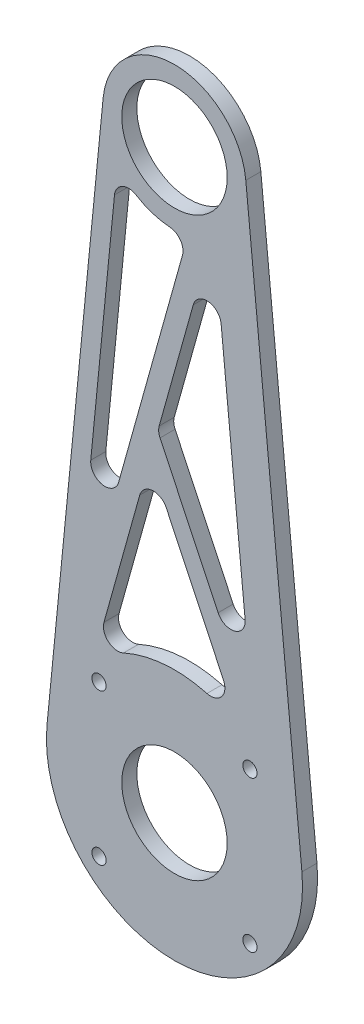
SolidWorks part; units mm, degrees
ref_plane "Front Plane" through (0, 0, 0) normal (0, 0, 1) x (1, 0, 0)
ref_plane "Top Plane" through (0, 0, 0) normal (0, 1, 0) x (1, 0, 0)
ref_plane "Right Plane" through (0, 0, 0) normal (1, 0, 0) x (0, 0, -1)
sketch "Sketch1" plane through (0, 0, 0) normal (0, 0, 1) x (1, 0, 0)
  line L0 (-15.04, 122.9996) -> (-26.8705, 2.6412)
  line L1 (15.04, 122.9996) -> (26.8705, 2.6412)
  circle A1 centre (15.9099, 15.9099) radius 1.5
  circle A2 centre (15.9099, -15.9099) radius 1.5
  circle A3 centre (-15.9099, -15.9099) radius 1.5
  circle A4 centre (-15.9099, 15.9099) radius 1.5
  circle A5 centre (0, 0) radius 27
  circle A6 centre (0, 121.5212) radius 11.1125
  circle A7 centre (0, 121.5212) radius 15.1125
  circle A8 centre (0, 0) radius 11.1125
  point P14 (0, 0)
  dimension "D2" = 3
  dimension "D4" = 54
  dimension "D5" = 22.225
  dimension "D8" = 22.225
  dimension "D7" = 121.5212
  dimension "D6" = 4
  dimension "D3" = 4
extrude "Boss-Extrude1" add sketch "Sketch1" along normal blind 3.175 contours A5 A8 A1 A2 A3 A4 | A7 L0 A5 L1 | A7 A6
sketch "Sketch2" plane through (0, 0, 0) normal (0, 0, -1) x (-1, 0, 0)
  line L5 (21.0059, 21.4147) -> (-2.8164, 106.6735)
  line L6 (22.8897, 2.2499) -> (11.0592, 122.6083)
  line L7 (-11.0592, 122.6083) -> (-22.8897, 2.2499)
  line L8 (21.0059, 21.4147) -> (12.0611, 112.4153)
  line L11 (2.5385, 65.8517) -> (3.525, 67.9304)
  line L12 (-8.2664, 110.131) -> (-16.5783, 25.5689)
  line L13 (3.525, 67.9304) -> (-8.2664, 110.131)
  line L14 (2.5385, 65.8517) -> (-16.5783, 25.5689)
  line L15 (16.9571, 19.8575) -> (5.1657, 62.0581)
  line L16 (5.1657, 62.0581) -> (-13.7499, 22.1992)
  arc A1 (16.9571, 19.8575) -> (-13.7499, 22.1992) centre (0, 0) ccw
  arc A4 (-22.8897, 2.2499) -> (22.8897, 2.2499) centre (0, 0) ccw
  arc A5 (11.0592, 122.6083) -> (-11.0592, 122.6083) centre (0, 121.5212) ccw
  circle A14 centre (0, 121.5212) radius 15.1125
  arc A15 (-2.8164, 106.6735) -> (12.0611, 112.4153) centre (0, 121.5212) ccw
  dimension "D1" = 4
  dimension "D2" = 4
extrude "Cut-Extrude1" cut sketch "Sketch2" against normal blind 3.175
fillet "Fillet1" radius 3 9 edges at (-21.0059, 21.4147, 1.5875) (2.8164, 106.6735, 1.5875) (-12.0611, 112.4153, 1.5875) (8.2664, 110.131, 1.5875) (16.5783, 25.5689, 1.5875) (-3.525, 67.9304, 1.5875) (-5.1657, 62.0581, 1.5875) (13.7499, 22.1992, 1.5875) (-16.9571, 19.8575, 1.5875)
